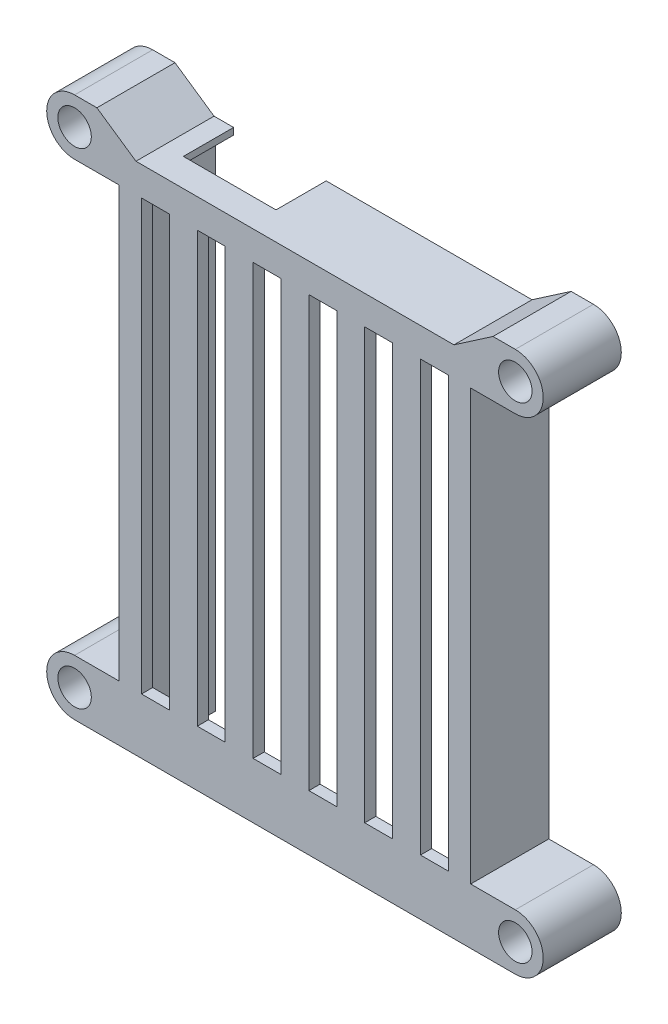
SolidWorks part; units mm, degrees
other "标注1"
sketch "草图12" plane through (84, -10, -12) normal (0.2939, -0.3316, -0.8965) x (0.9529, 0.0281, 0.302)
ref_plane "Front" through (0, 0, 0) normal (0, 0, 1) x (1, 0, 0)
ref_plane "Top" through (0, 0, 0) normal (0, 1, 0) x (1, 0, 0)
ref_plane "Right" through (0, 0, 0) normal (1, 0, 0) x (0, 0, -1)
sketch "草图1" plane through (0, 0, 0) normal (0, 0, 1) x (1, 0, 0)
  line L0 (0, 0) -> (8, 0)
  line L1 (8, 0) -> (8, 77)
  line L2 (8, 77) -> (0, 77)
  line L3 (0, -10) -> (8, -10)
  line L7 (71, -10) -> (79, -10)
  line L8 (79, 0) -> (71, 0)
  line L9 (71, 0) -> (71, 77)
  line L10 (71, 77) -> (79, 77)
  line L11 (0, 87) -> (79, 87)
  line L12 (8, -10) -> (71, -10)
  arc A0 (0, 0) -> (0, -10) centre (0, -5) ccw
  arc A1 (79, -10) -> (79, 0) centre (79, -5) ccw
  arc A2 (0, 77) -> (0, 87) centre (0, 82) cw
  arc A3 (79, 87) -> (79, 77) centre (79, 82) cw
  dimension "D1" = 5
  dimension "D2" = 5
  dimension "D3" = 5
  dimension "D4" = 8
  dimension "D14" = 63
  dimension "D5" = 8
  dimension "D6" = 8
  dimension "D7" = 8
  dimension "D10" = 63
  dimension "D11" = 92
extrude "凸台-拉伸1" add sketch "草图1" along normal blind 2 contours L11 A3 L10 L9 L8 A1 L7 L12 L3 A0 L0 L1 L2 A2
sketch "草图4" plane through (0, 0, 0) normal (0, 0, -1) x (-1, 0, 0)
  line L0 (0, 87) -> (-79, 87) construction
  line L1 (-11.3, -10) -> (-67.7, -10)
  line L2 (-11.3, -10) -> (-11.3, 81)
  line L3 (-11.3, 81) -> (-67.7, 81)
  line L4 (-67.7, -10) -> (-67.7, 81)
  line L6 (0, -10) -> (-79, -10) construction
  line L7 (-8, 0) -> (-8, 77) construction
  point P0 (-39.5, 38.5)
  point P8 (-39.5, 87)
  point P12 (-8, 38.5)
  dimension "D1" = 0
  dimension "D2" = 56.4
  dimension "D3" = 6
extrude "凸台-拉伸2" add sketch "草图4" along normal blind 12
sketch "草图5" plane through (0, 0, 2) normal (0, 0, 1) x (1, 0, 0)
  circle A0 centre (79, 82) radius 3
  circle A1 centre (0, 82) radius 3
  circle A2 centre (79, -5) radius 3
  circle A3 centre (0, -5) radius 3
  dimension "D1" = 6
  dimension "D2" = 6
  dimension "D3" = 6
  dimension "D4" = 6
extrude "切除-拉伸1" cut sketch "草图5" against normal through all
sketch "草图8" plane through (0, 81, 0) normal (0, -1, 0) x (1, 0, 0)
  line L0 (14.5, -12) -> (31.1, -12)
  line L1 (14.5, -12) -> (14.5, -3)
  line L2 (31.1, -12) -> (31.1, -3)
  line L3 (14.5, -3) -> (31.1, -3)
  line L4 (11.3, -12) -> (67.7, -12) construction
  dimension "D1" = 9
  dimension "D2" = 16.6
  dimension "D3" = 3.2
extrude "切除-拉伸3" cut sketch "草图8" against normal through all
sketch "草图10" plane through (0, 0, -12) normal (0, 0, -1) x (-1, 0, 0)
  line L0 (-75.0018, 87) -> (-68.0018, 82.2)
  line L1 (-31.1, 87) -> (-79, 87) construction
  line L2 (-68.0018, 82.2) -> (-11, 82.2)
  line L3 (-11, 82.2) -> (-4, 87)
  line L5 (0, 87) -> (-14.5, 87) construction
  circle A0 centre (-79, 82) radius 3 construction
  circle A1 centre (0, 82) radius 3 construction
  dimension "D1" = 4.8
  dimension "D2" = 7
  dimension "D3" = 11
  dimension "D4" = 11
  dimension "D5" = 7
extrude "切除-拉伸5" cut sketch "草图10" against normal through all and the other way through all
sketch "草图11" plane through (0, 0, 2) normal (0, 0, 1) x (1, 0, 0)
  line L0 (12, 77) -> (67, 77)
  line L1 (12, 77) -> (12, 0)
  line L2 (67, 77) -> (67, 0)
  line L3 (12, 0) -> (67, 0)
  line L4 (0, 0) -> (8, 0) construction
  line L5 (8, 0) -> (8, 77) construction
  line L6 (71, 0) -> (71, 77) construction
  line L7 (17, 77) -> (17, 0)
  line L8 (22, 77) -> (22, 0)
  line L9 (62, 77) -> (62, 0)
  line L10 (27, 77) -> (27, 0)
  line L11 (32, 77) -> (32, 0)
  line L12 (37, 77) -> (37, 0)
  line L13 (42, 77) -> (42, 0)
  line L14 (47, 77) -> (47, 0)
  line L15 (52, 77) -> (52, 0)
  line L16 (57, 77) -> (57, 0)
  dimension "D1" = 4
  dimension "D2" = 4
  dimension "D3" = 5
  dimension "D4" = 5
  dimension "D5" = 5
  dimension "D6" = 5
  dimension "D7" = 5
  dimension "D8" = 5
  dimension "D9" = 5
  dimension "D10" = 5
  dimension "D11" = 5
  dimension "D12" = 5
extrude "切除-拉伸6" cut sketch "草图11" against normal blind 2 contours L7 L0 L1 L3 | L10 L0 L8 L3 | L12 L0 L11 L3 | L14 L0 L13 L3 | L16 L0 L15 L3 | L0 L9 L3 L2
